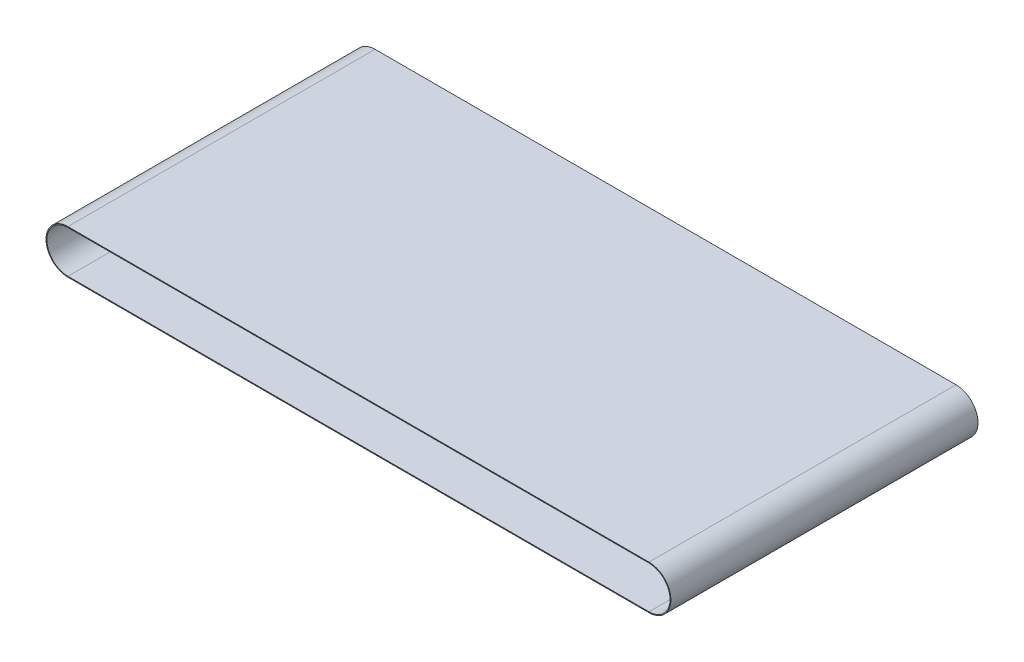
SolidWorks part; units mm, degrees
ref_plane "前视基准面" through (0, 0, 0) normal (0, 0, 1) x (1, 0, 0)
ref_plane "上视基准面" through (0, 0, 0) normal (0, 1, 0) x (1, 0, 0)
ref_plane "右视基准面" through (0, 0, 0) normal (1, 0, 0) x (0, 0, -1)
sketch "草图1" plane through (0, 0, -202.8978) normal (0, 0, -1) x (-1, 0, 0)
  line L0 (80.5605, 160.574) -> (780.5605, 160.574)
  line L1 (780.5605, 110.574) -> (80.5605, 110.574)
  circle A0 centre (80.5605, 135.574) radius 25 construction
  arc A1 (80.5605, 160.574) -> (80.5605, 110.574) centre (80.5605, 135.574) ccw
  circle A2 centre (780.5605, 135.574) radius 25 construction
  arc A3 (780.5605, 110.574) -> (780.5605, 160.574) centre (780.5605, 135.574) ccw
ref_plane "基准面1" through (-80.5605, 0, 0) normal (1, 0, 0) x (0, 0, -1)
sketch "草图2" plane through (-80.5605, 0, 0) normal (1, 0, 0) x (0, 0, -1)
  line L1 (-167.1022, 161) -> (202.8978, 161)
  line L2 (-167.1022, 161) -> (-167.1022, 162)
  line L3 (-167.1022, 162) -> (202.8978, 162)
  line L4 (202.8978, 161) -> (202.8978, 162)
  line L6 (202.8978, 110.574) -> (202.8978, 160.574) construction
  dimension "D1" = 1
  dimension "D2" = 370
  dimension "D4" = 162
sweep "扫描1" add profiles "草图2" path "草图1"
